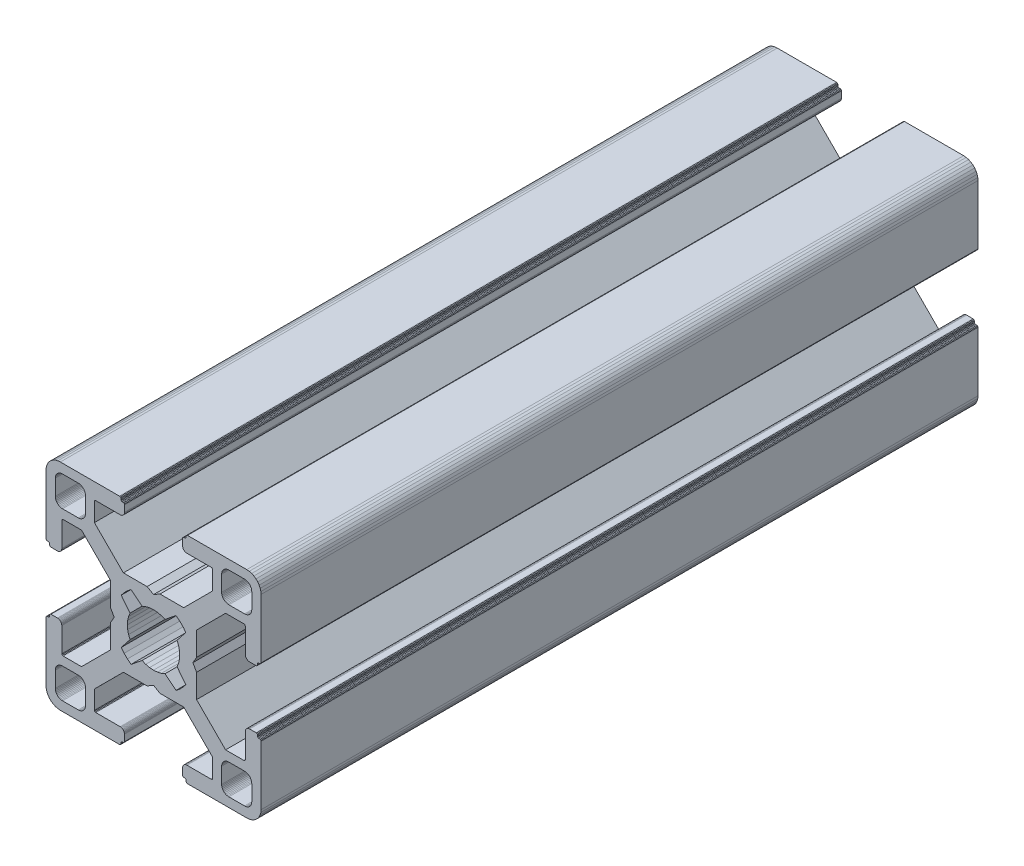
SolidWorks part; units mm, degrees
ref_plane "Front Plane" through (0, 0, 0) normal (0, 0, 1) x (1, 0, 0)
ref_plane "Top Plane" through (0, 0, 0) normal (0, 1, 0) x (1, 0, 0)
ref_plane "Right Plane" through (0, 0, 0) normal (1, 0, 0) x (0, 0, -1)
ref_plane "Plane1" through (0, 0, 0) normal (0, 0, 1) x (1, 0, 0)
sketch "Sketch1" plane through (0, 0, 0) normal (0, 0, 1) x (1, 0, 0)
  line L0 (28.3473, 29.9696) -> (28, 30)
  line L1 (28, 30) -> (19.75, 30)
  line L2 (19.75, 30) -> (19.7153, 29.997)
  line L3 (19.7153, 29.997) -> (19.6816, 29.9879)
  line L4 (19.6816, 29.9879) -> (19.65, 29.9732)
  line L5 (19.65, 29.9732) -> (19.6214, 29.9532)
  line L6 (19.6214, 29.9532) -> (19.5968, 29.9286)
  line L7 (19.5968, 29.9286) -> (19.5768, 29.9)
  line L8 (19.5768, 29.9) -> (19.5621, 29.8684)
  line L9 (19.5621, 29.8684) -> (19.553, 29.8347)
  line L10 (19.553, 29.8347) -> (19.55, 29.8)
  line L11 (19.55, 29.8) -> (19.55, 29.7)
  line L12 (19.55, 29.7) -> (19.547, 29.6653)
  line L13 (19.547, 29.6653) -> (19.5379, 29.6316)
  line L14 (19.5379, 29.6316) -> (19.5232, 29.6)
  line L15 (19.5232, 29.6) -> (19.5032, 29.5714)
  line L16 (19.5032, 29.5714) -> (19.4786, 29.5468)
  line L17 (19.4786, 29.5468) -> (19.45, 29.5268)
  line L18 (19.45, 29.5268) -> (19.4184, 29.5121)
  line L19 (19.4184, 29.5121) -> (19.3847, 29.503)
  line L20 (19.3847, 29.503) -> (19.35, 29.5)
  line L21 (19.35, 29.5) -> (19.25, 29.5)
  line L22 (19.25, 29.5) -> (19.2153, 29.497)
  line L23 (19.2153, 29.497) -> (19.1816, 29.4879)
  line L24 (19.1816, 29.4879) -> (19.15, 29.4732)
  line L25 (19.15, 29.4732) -> (19.1214, 29.4532)
  line L26 (19.1214, 29.4532) -> (19.0968, 29.4286)
  line L27 (19.0968, 29.4286) -> (19.0768, 29.4)
  line L28 (19.0768, 29.4) -> (19.0621, 29.3684)
  line L29 (19.0621, 29.3684) -> (19.053, 29.3347)
  line L30 (19.053, 29.3347) -> (19.05, 29.3)
  line L31 (19.05, 29.3) -> (19.05, 28.4)
  line L32 (19.05, 28.4) -> (19.0591, 28.2958)
  line L33 (19.0591, 28.2958) -> (19.0862, 28.1948)
  line L34 (19.0862, 28.1948) -> (19.1304, 28.1)
  line L35 (19.1304, 28.1) -> (19.1904, 28.0143)
  line L36 (19.1904, 28.0143) -> (19.2643, 27.9404)
  line L37 (19.2643, 27.9404) -> (19.35, 27.8804)
  line L38 (19.35, 27.8804) -> (19.4448, 27.8362)
  line L39 (19.4448, 27.8362) -> (19.5458, 27.8091)
  line L40 (19.5458, 27.8091) -> (19.65, 27.8)
  line L41 (19.65, 27.8) -> (23.05, 27.8)
  line L42 (23.05, 27.8) -> (23.0847, 27.7969)
  line L43 (23.0847, 27.7969) -> (23.1184, 27.7879)
  line L44 (23.1184, 27.7879) -> (23.15, 27.7732)
  line L45 (23.15, 27.7732) -> (23.1786, 27.7532)
  line L46 (23.1786, 27.7532) -> (23.2032, 27.7285)
  line L47 (23.2032, 27.7285) -> (23.2232, 27.7)
  line L48 (23.2232, 27.7) -> (23.2379, 27.6684)
  line L49 (23.2379, 27.6684) -> (23.247, 27.6347)
  line L50 (23.247, 27.6347) -> (23.25, 27.6)
  line L51 (23.25, 27.6) -> (23.25, 25.05)
  line L52 (23.25, 25.05) -> (19.2045, 21)
  line L53 (19.2045, 21) -> (15.9, 21)
  line L54 (15.9, 21) -> (15, 20.4848)
  line L55 (15, 20.4848) -> (14.1, 21)
  line L56 (14.1, 21) -> (10.7955, 21)
  line L57 (10.7955, 21) -> (7.9973, 23.8013)
  line L58 (7.9973, 23.8013) -> (6.75, 25.05)
  line L59 (6.75, 25.05) -> (6.75, 27.6)
  line L60 (6.75, 27.6) -> (6.753, 27.6347)
  line L61 (6.753, 27.6347) -> (6.7621, 27.6684)
  line L62 (6.7621, 27.6684) -> (6.7768, 27.7)
  line L63 (6.7768, 27.7) -> (6.7968, 27.7285)
  line L64 (6.7968, 27.7285) -> (6.8215, 27.7532)
  line L65 (6.8215, 27.7532) -> (6.85, 27.7732)
  line L66 (6.85, 27.7732) -> (6.8816, 27.7879)
  line L67 (6.8816, 27.7879) -> (6.9153, 27.7969)
  line L68 (6.9153, 27.7969) -> (6.95, 27.8)
  line L69 (6.95, 27.8) -> (10.35, 27.8)
  line L70 (10.35, 27.8) -> (10.4542, 27.8091)
  line L71 (10.4542, 27.8091) -> (10.5552, 27.8362)
  line L72 (10.5552, 27.8362) -> (10.65, 27.8804)
  line L73 (10.65, 27.8804) -> (10.7357, 27.9404)
  line L74 (10.7357, 27.9404) -> (10.8096, 28.0143)
  line L75 (10.8096, 28.0143) -> (10.8696, 28.1)
  line L76 (10.8696, 28.1) -> (10.9138, 28.1948)
  line L77 (10.9138, 28.1948) -> (10.9409, 28.2958)
  line L78 (10.9409, 28.2958) -> (10.95, 28.4)
  line L79 (10.95, 28.4) -> (10.95, 29.3)
  line L80 (10.95, 29.3) -> (10.947, 29.3347)
  line L81 (10.947, 29.3347) -> (10.938, 29.3684)
  line L82 (10.938, 29.3684) -> (10.9232, 29.4)
  line L83 (10.9232, 29.4) -> (10.9032, 29.4286)
  line L84 (10.9032, 29.4286) -> (10.8786, 29.4532)
  line L85 (10.8786, 29.4532) -> (10.85, 29.4732)
  line L86 (10.85, 29.4732) -> (10.8184, 29.4879)
  line L87 (10.8184, 29.4879) -> (10.7847, 29.497)
  line L88 (10.7847, 29.497) -> (10.75, 29.5)
  line L89 (10.75, 29.5) -> (10.65, 29.5)
  line L90 (10.65, 29.5) -> (10.6153, 29.503)
  line L91 (10.6153, 29.503) -> (10.5816, 29.5121)
  line L92 (10.5816, 29.5121) -> (10.55, 29.5268)
  line L93 (10.55, 29.5268) -> (10.5214, 29.5468)
  line L94 (10.5214, 29.5468) -> (10.4968, 29.5714)
  line L95 (10.4968, 29.5714) -> (10.4768, 29.6)
  line L96 (10.4768, 29.6) -> (10.4621, 29.6316)
  line L97 (10.4621, 29.6316) -> (10.453, 29.6653)
  line L98 (10.453, 29.6653) -> (10.45, 29.7)
  line L99 (10.45, 29.7) -> (10.45, 29.8)
  line L100 (10.45, 29.8) -> (10.447, 29.8347)
  line L101 (10.447, 29.8347) -> (10.4379, 29.8684)
  line L102 (10.4379, 29.8684) -> (10.4232, 29.9)
  line L103 (10.4232, 29.9) -> (10.4032, 29.9286)
  line L104 (10.4032, 29.9286) -> (10.3786, 29.9532)
  line L105 (10.3786, 29.9532) -> (10.35, 29.9732)
  line L106 (10.35, 29.9732) -> (10.3184, 29.9879)
  line L107 (10.3184, 29.9879) -> (10.2847, 29.997)
  line L108 (10.2847, 29.997) -> (10.25, 30)
  line L109 (10.25, 30) -> (2, 30)
  line L110 (2, 30) -> (1.6527, 29.9696)
  line L111 (1.6527, 29.9696) -> (1.316, 29.8794)
  line L112 (1.316, 29.8794) -> (1, 29.7321)
  line L113 (1, 29.7321) -> (0.7144, 29.5321)
  line L114 (0.7144, 29.5321) -> (0.4679, 29.2856)
  line L115 (0.4679, 29.2856) -> (0.2679, 29)
  line L116 (0.2679, 29) -> (0.1206, 28.684)
  line L117 (0.1206, 28.684) -> (0.0304, 28.3473)
  line L118 (0.0304, 28.3473) -> (0, 28)
  line L119 (0, 28) -> (0, 19.75)
  line L120 (0, 19.75) -> (0.003, 19.7153)
  line L121 (0.003, 19.7153) -> (0.0121, 19.6816)
  line L122 (0.0121, 19.6816) -> (0.0268, 19.65)
  line L123 (0.0268, 19.65) -> (0.0468, 19.6214)
  line L124 (0.0468, 19.6214) -> (0.0714, 19.5968)
  line L125 (0.0714, 19.5968) -> (0.1, 19.5768)
  line L126 (0.1, 19.5768) -> (0.1316, 19.5621)
  line L127 (0.1316, 19.5621) -> (0.1653, 19.553)
  line L128 (0.1653, 19.553) -> (0.2, 19.55)
  line L129 (0.2, 19.55) -> (0.3, 19.55)
  line L130 (0.3, 19.55) -> (0.3347, 19.547)
  line L131 (0.3347, 19.547) -> (0.3684, 19.5379)
  line L132 (0.3684, 19.5379) -> (0.4, 19.5232)
  line L133 (0.4, 19.5232) -> (0.4286, 19.5032)
  line L134 (0.4286, 19.5032) -> (0.4532, 19.4786)
  line L135 (0.4532, 19.4786) -> (0.4732, 19.45)
  line L136 (0.4732, 19.45) -> (0.4879, 19.4184)
  line L137 (0.4879, 19.4184) -> (0.497, 19.3847)
  line L138 (0.497, 19.3847) -> (0.5, 19.35)
  line L139 (0.5, 19.35) -> (0.5, 19.25)
  line L140 (0.5, 19.25) -> (0.503, 19.2153)
  line L141 (0.503, 19.2153) -> (0.5121, 19.1816)
  line L142 (0.5121, 19.1816) -> (0.5268, 19.15)
  line L143 (0.5268, 19.15) -> (0.5468, 19.1214)
  line L144 (0.5468, 19.1214) -> (0.5714, 19.0968)
  line L145 (0.5714, 19.0968) -> (0.6, 19.0768)
  line L146 (0.6, 19.0768) -> (0.6316, 19.0621)
  line L147 (0.6316, 19.0621) -> (0.6653, 19.053)
  line L148 (0.6653, 19.053) -> (0.7, 19.05)
  line L149 (0.7, 19.05) -> (1.6, 19.05)
  line L150 (1.6, 19.05) -> (1.7042, 19.0591)
  line L151 (1.7042, 19.0591) -> (1.8052, 19.0862)
  line L152 (1.8052, 19.0862) -> (1.9, 19.1304)
  line L153 (1.9, 19.1304) -> (1.9857, 19.1904)
  line L154 (1.9857, 19.1904) -> (2.0596, 19.2643)
  line L155 (2.0596, 19.2643) -> (2.1196, 19.35)
  line L156 (2.1196, 19.35) -> (2.1638, 19.4448)
  line L157 (2.1638, 19.4448) -> (2.1909, 19.5458)
  line L158 (2.1909, 19.5458) -> (2.2, 19.65)
  line L159 (2.2, 19.65) -> (2.2, 23.05)
  line L160 (2.2, 23.05) -> (2.203, 23.0847)
  line L161 (2.203, 23.0847) -> (2.2121, 23.1184)
  line L162 (2.2121, 23.1184) -> (2.2268, 23.15)
  line L163 (2.2268, 23.15) -> (2.2468, 23.1786)
  line L164 (2.2468, 23.1786) -> (2.2714, 23.2032)
  line L165 (2.2714, 23.2032) -> (2.3, 23.2232)
  line L166 (2.3, 23.2232) -> (2.3316, 23.2379)
  line L167 (2.3316, 23.2379) -> (2.3653, 23.247)
  line L168 (2.3653, 23.247) -> (2.4, 23.25)
  line L169 (2.4, 23.25) -> (4.95, 23.25)
  line L170 (4.95, 23.25) -> (7.9973, 20.2027)
  line L171 (7.9973, 20.2027) -> (8.9955, 19.2045)
  line L172 (8.9955, 19.2045) -> (8.9955, 15.9)
  line L173 (8.9955, 15.9) -> (9.5151, 15)
  line L174 (9.5151, 15) -> (8.9955, 14.1)
  line L175 (8.9955, 14.1) -> (8.9955, 10.7955)
  line L176 (8.9955, 10.7955) -> (4.95, 6.75)
  line L177 (4.95, 6.75) -> (2.4, 6.75)
  line L178 (2.4, 6.75) -> (2.3653, 6.753)
  line L179 (2.3653, 6.753) -> (2.3316, 6.7621)
  line L180 (2.3316, 6.7621) -> (2.3, 6.7768)
  line L181 (2.3, 6.7768) -> (2.2714, 6.7968)
  line L182 (2.2714, 6.7968) -> (2.2468, 6.8214)
  line L183 (2.2468, 6.8214) -> (2.2268, 6.85)
  line L184 (2.2268, 6.85) -> (2.2121, 6.8816)
  line L185 (2.2121, 6.8816) -> (2.203, 6.9153)
  line L186 (2.203, 6.9153) -> (2.2, 6.95)
  line L187 (2.2, 6.95) -> (2.2, 10.35)
  line L188 (2.2, 10.35) -> (2.1909, 10.4542)
  line L189 (2.1909, 10.4542) -> (2.1638, 10.5552)
  line L190 (2.1638, 10.5552) -> (2.1196, 10.65)
  line L191 (2.1196, 10.65) -> (2.0596, 10.7357)
  line L192 (2.0596, 10.7357) -> (1.9857, 10.8096)
  line L193 (1.9857, 10.8096) -> (1.9, 10.8696)
  line L194 (1.9, 10.8696) -> (1.8052, 10.9138)
  line L195 (1.8052, 10.9138) -> (1.7042, 10.9409)
  line L196 (1.7042, 10.9409) -> (1.6, 10.95)
  line L197 (1.6, 10.95) -> (0.7, 10.95)
  line L198 (0.7, 10.95) -> (0.6653, 10.9469)
  line L199 (0.6653, 10.9469) -> (0.6316, 10.9379)
  line L200 (0.6316, 10.9379) -> (0.6, 10.9232)
  line L201 (0.6, 10.9232) -> (0.5715, 10.9032)
  line L202 (0.5715, 10.9032) -> (0.5468, 10.8785)
  line L203 (0.5468, 10.8785) -> (0.5268, 10.85)
  line L204 (0.5268, 10.85) -> (0.5121, 10.8184)
  line L205 (0.5121, 10.8184) -> (0.503, 10.7847)
  line L206 (0.503, 10.7847) -> (0.5, 10.75)
  line L207 (0.5, 10.75) -> (0.5, 10.65)
  line L208 (0.5, 10.65) -> (0.497, 10.6153)
  line L209 (0.497, 10.6153) -> (0.4879, 10.5816)
  line L210 (0.4879, 10.5816) -> (0.4732, 10.55)
  line L211 (0.4732, 10.55) -> (0.4532, 10.5214)
  line L212 (0.4532, 10.5214) -> (0.4286, 10.4968)
  line L213 (0.4286, 10.4968) -> (0.4, 10.4768)
  line L214 (0.4, 10.4768) -> (0.3684, 10.4621)
  line L215 (0.3684, 10.4621) -> (0.3347, 10.453)
  line L216 (0.3347, 10.453) -> (0.3, 10.45)
  line L217 (0.3, 10.45) -> (0.2, 10.45)
  line L218 (0.2, 10.45) -> (0.1653, 10.447)
  line L219 (0.1653, 10.447) -> (0.1316, 10.4379)
  line L220 (0.1316, 10.4379) -> (0.1, 10.4232)
  line L221 (0.1, 10.4232) -> (0.0714, 10.4032)
  line L222 (0.0714, 10.4032) -> (0.0468, 10.3786)
  line L223 (0.0468, 10.3786) -> (0.0268, 10.35)
  line L224 (0.0268, 10.35) -> (0.0121, 10.3184)
  line L225 (0.0121, 10.3184) -> (0.003, 10.2847)
  line L226 (0.003, 10.2847) -> (0, 10.25)
  line L227 (0, 10.25) -> (0, 2)
  line L228 (0, 2) -> (0.0304, 1.6527)
  line L229 (0.0304, 1.6527) -> (0.1206, 1.316)
  line L230 (0.1206, 1.316) -> (0.2679, 1)
  line L231 (0.2679, 1) -> (0.4679, 0.7144)
  line L232 (0.4679, 0.7144) -> (0.7144, 0.4679)
  line L233 (0.7144, 0.4679) -> (1, 0.2679)
  line L234 (1, 0.2679) -> (1.316, 0.1206)
  line L235 (1.316, 0.1206) -> (1.6527, 0.0304)
  line L236 (1.6527, 0.0304) -> (2, 0)
  line L237 (2, 0) -> (10.25, 0)
  line L238 (10.25, 0) -> (10.2847, 0.003)
  line L239 (10.2847, 0.003) -> (10.3184, 0.0121)
  line L240 (10.3184, 0.0121) -> (10.35, 0.0268)
  line L241 (10.35, 0.0268) -> (10.3786, 0.0468)
  line L242 (10.3786, 0.0468) -> (10.4032, 0.0714)
  line L243 (10.4032, 0.0714) -> (10.4232, 0.1)
  line L244 (10.4232, 0.1) -> (10.4379, 0.1316)
  line L245 (10.4379, 0.1316) -> (10.447, 0.1653)
  line L246 (10.447, 0.1653) -> (10.45, 0.2)
  line L247 (10.45, 0.2) -> (10.45, 0.3)
  line L248 (10.45, 0.3) -> (10.453, 0.3347)
  line L249 (10.453, 0.3347) -> (10.4621, 0.3684)
  line L250 (10.4621, 0.3684) -> (10.4768, 0.4)
  line L251 (10.4768, 0.4) -> (10.4968, 0.4286)
  line L252 (10.4968, 0.4286) -> (10.5214, 0.4532)
  line L253 (10.5214, 0.4532) -> (10.55, 0.4732)
  line L254 (10.55, 0.4732) -> (10.5816, 0.4879)
  line L255 (10.5816, 0.4879) -> (10.6153, 0.497)
  line L256 (10.6153, 0.497) -> (10.65, 0.5)
  line L257 (10.65, 0.5) -> (10.75, 0.5)
  line L258 (10.75, 0.5) -> (10.7847, 0.503)
  line L259 (10.7847, 0.503) -> (10.8184, 0.5121)
  line L260 (10.8184, 0.5121) -> (10.85, 0.5268)
  line L261 (10.85, 0.5268) -> (10.8785, 0.5468)
  line L262 (10.8785, 0.5468) -> (10.9032, 0.5715)
  line L263 (10.9032, 0.5715) -> (10.9232, 0.6)
  line L264 (10.9232, 0.6) -> (10.9379, 0.6316)
  line L265 (10.9379, 0.6316) -> (10.9469, 0.6653)
  line L266 (10.9469, 0.6653) -> (10.95, 0.7)
  line L267 (10.95, 0.7) -> (10.95, 1.6)
  line L268 (10.95, 1.6) -> (10.9409, 1.7042)
  line L269 (10.9409, 1.7042) -> (10.9138, 1.8052)
  line L270 (10.9138, 1.8052) -> (10.8696, 1.9)
  line L271 (10.8696, 1.9) -> (10.8096, 1.9857)
  line L272 (10.8096, 1.9857) -> (10.7357, 2.0596)
  line L273 (10.7357, 2.0596) -> (10.65, 2.1196)
  line L274 (10.65, 2.1196) -> (10.5552, 2.1638)
  line L275 (10.5552, 2.1638) -> (10.4542, 2.1909)
  line L276 (10.4542, 2.1909) -> (10.35, 2.2)
  line L277 (10.35, 2.2) -> (6.95, 2.2)
  line L278 (6.95, 2.2) -> (6.9153, 2.203)
  line L279 (6.9153, 2.203) -> (6.8816, 2.212)
  line L280 (6.8816, 2.212) -> (6.85, 2.2268)
  line L281 (6.85, 2.2268) -> (6.8215, 2.2468)
  line L282 (6.8215, 2.2468) -> (6.7968, 2.2714)
  line L283 (6.7968, 2.2714) -> (6.7768, 2.3)
  line L284 (6.7768, 2.3) -> (6.7621, 2.3316)
  line L285 (6.7621, 2.3316) -> (6.753, 2.3653)
  line L286 (6.753, 2.3653) -> (6.75, 2.4)
  line L287 (6.75, 2.4) -> (6.75, 4.95)
  line L288 (6.75, 4.95) -> (9.7875, 7.9908)
  line L289 (9.7875, 7.9908) -> (10.7955, 9)
  line L290 (10.7955, 9) -> (14.1, 9)
  line L291 (14.1, 9) -> (15, 9.5151)
  line L292 (15, 9.5151) -> (15.9, 9)
  line L293 (15.9, 9) -> (19.2045, 9)
  line L294 (19.2045, 9) -> (20.2126, 7.9908)
  line L295 (20.2126, 7.9908) -> (23.25, 4.95)
  line L296 (23.25, 4.95) -> (23.25, 2.4)
  line L297 (23.25, 2.4) -> (23.247, 2.3653)
  line L298 (23.247, 2.3653) -> (23.2379, 2.3316)
  line L299 (23.2379, 2.3316) -> (23.2232, 2.3)
  line L300 (23.2232, 2.3) -> (23.2032, 2.2714)
  line L301 (23.2032, 2.2714) -> (23.1786, 2.2468)
  line L302 (23.1786, 2.2468) -> (23.15, 2.2268)
  line L303 (23.15, 2.2268) -> (23.1184, 2.212)
  line L304 (23.1184, 2.212) -> (23.0847, 2.203)
  line L305 (23.0847, 2.203) -> (23.05, 2.2)
  line L306 (23.05, 2.2) -> (19.65, 2.2)
  line L307 (19.65, 2.2) -> (19.5458, 2.1909)
  line L308 (19.5458, 2.1909) -> (19.4448, 2.1638)
  line L309 (19.4448, 2.1638) -> (19.35, 2.1196)
  line L310 (19.35, 2.1196) -> (19.2643, 2.0596)
  line L311 (19.2643, 2.0596) -> (19.1904, 1.9857)
  line L312 (19.1904, 1.9857) -> (19.1304, 1.9)
  line L313 (19.1304, 1.9) -> (19.0862, 1.8052)
  line L314 (19.0862, 1.8052) -> (19.0591, 1.7042)
  line L315 (19.0591, 1.7042) -> (19.05, 1.6)
  line L316 (19.05, 1.6) -> (19.05, 0.7)
  line L317 (19.05, 0.7) -> (19.053, 0.6653)
  line L318 (19.053, 0.6653) -> (19.0621, 0.6316)
  line L319 (19.0621, 0.6316) -> (19.0768, 0.6)
  line L320 (19.0768, 0.6) -> (19.0968, 0.5714)
  line L321 (19.0968, 0.5714) -> (19.1214, 0.5468)
  line L322 (19.1214, 0.5468) -> (19.15, 0.5268)
  line L323 (19.15, 0.5268) -> (19.1816, 0.5121)
  line L324 (19.1816, 0.5121) -> (19.2153, 0.503)
  line L325 (19.2153, 0.503) -> (19.25, 0.5)
  line L326 (19.25, 0.5) -> (19.35, 0.5)
  line L327 (19.35, 0.5) -> (19.3847, 0.497)
  line L328 (19.3847, 0.497) -> (19.4184, 0.4879)
  line L329 (19.4184, 0.4879) -> (19.45, 0.4732)
  line L330 (19.45, 0.4732) -> (19.4786, 0.4532)
  line L331 (19.4786, 0.4532) -> (19.5032, 0.4286)
  line L332 (19.5032, 0.4286) -> (19.5232, 0.4)
  line L333 (19.5232, 0.4) -> (19.5379, 0.3684)
  line L334 (19.5379, 0.3684) -> (19.547, 0.3347)
  line L335 (19.547, 0.3347) -> (19.55, 0.3)
  line L336 (19.55, 0.3) -> (19.55, 0.2)
  line L337 (19.55, 0.2) -> (19.553, 0.1653)
  line L338 (19.553, 0.1653) -> (19.5621, 0.1316)
  line L339 (19.5621, 0.1316) -> (19.5768, 0.1)
  line L340 (19.5768, 0.1) -> (19.5968, 0.0714)
  line L341 (19.5968, 0.0714) -> (19.6214, 0.0468)
  line L342 (19.6214, 0.0468) -> (19.65, 0.0268)
  line L343 (19.65, 0.0268) -> (19.6816, 0.0121)
  line L344 (19.6816, 0.0121) -> (19.7153, 0.003)
  line L345 (19.7153, 0.003) -> (19.75, 0)
  line L346 (19.75, 0) -> (28, 0)
  line L347 (28, 0) -> (28.3473, 0.0304)
  line L348 (28.3473, 0.0304) -> (28.684, 0.1206)
  line L349 (28.684, 0.1206) -> (29, 0.2679)
  line L350 (29, 0.2679) -> (29.2856, 0.4679)
  line L351 (29.2856, 0.4679) -> (29.5321, 0.7144)
  line L352 (29.5321, 0.7144) -> (29.7321, 1)
  line L353 (29.7321, 1) -> (29.8794, 1.316)
  line L354 (29.8794, 1.316) -> (29.9696, 1.6527)
  line L355 (29.9696, 1.6527) -> (30, 2)
  line L356 (30, 2) -> (30, 10.25)
  line L357 (30, 10.25) -> (29.997, 10.2847)
  line L358 (29.997, 10.2847) -> (29.988, 10.3184)
  line L359 (29.988, 10.3184) -> (29.9732, 10.35)
  line L360 (29.9732, 10.35) -> (29.9532, 10.3785)
  line L361 (29.9532, 10.3785) -> (29.9286, 10.4032)
  line L362 (29.9286, 10.4032) -> (29.9, 10.4232)
  line L363 (29.9, 10.4232) -> (29.8684, 10.4379)
  line L364 (29.8684, 10.4379) -> (29.8347, 10.447)
  line L365 (29.8347, 10.447) -> (29.8, 10.45)
  line L366 (29.8, 10.45) -> (29.7, 10.45)
  line L367 (29.7, 10.45) -> (29.6649, 10.4534)
  line L368 (29.6649, 10.4534) -> (29.6312, 10.4624)
  line L369 (29.6312, 10.4624) -> (29.5996, 10.4772)
  line L370 (29.5996, 10.4772) -> (29.5711, 10.4972)
  line L371 (29.5711, 10.4972) -> (29.5464, 10.5218)
  line L372 (29.5464, 10.5218) -> (29.5264, 10.5504)
  line L373 (29.5264, 10.5504) -> (29.5117, 10.582)
  line L374 (29.5117, 10.582) -> (29.5027, 10.6156)
  line L375 (29.5027, 10.6156) -> (29.4996, 10.6504)
  line L376 (29.4996, 10.6504) -> (29.4996, 10.7504)
  line L377 (29.4996, 10.7504) -> (29.497, 10.7847)
  line L378 (29.497, 10.7847) -> (29.4879, 10.8184)
  line L379 (29.4879, 10.8184) -> (29.4732, 10.85)
  line L380 (29.4732, 10.85) -> (29.4532, 10.8785)
  line L381 (29.4532, 10.8785) -> (29.4286, 10.9032)
  line L382 (29.4286, 10.9032) -> (29.4, 10.9232)
  line L383 (29.4, 10.9232) -> (29.3684, 10.9379)
  line L384 (29.3684, 10.9379) -> (29.3347, 10.9469)
  line L385 (29.3347, 10.9469) -> (29.3, 10.95)
  line L386 (29.3, 10.95) -> (28.4, 10.95)
  line L387 (28.4, 10.95) -> (28.2958, 10.9409)
  line L388 (28.2958, 10.9409) -> (28.1948, 10.9138)
  line L389 (28.1948, 10.9138) -> (28.1, 10.8696)
  line L390 (28.1, 10.8696) -> (28.0143, 10.8096)
  line L391 (28.0143, 10.8096) -> (27.9404, 10.7357)
  line L392 (27.9404, 10.7357) -> (27.8804, 10.65)
  line L393 (27.8804, 10.65) -> (27.8362, 10.5552)
  line L394 (27.8362, 10.5552) -> (27.8091, 10.4542)
  line L395 (27.8091, 10.4542) -> (27.8, 10.35)
  line L396 (27.8, 10.35) -> (27.8, 6.95)
  line L397 (27.8, 6.95) -> (27.797, 6.9153)
  line L398 (27.797, 6.9153) -> (27.7879, 6.8816)
  line L399 (27.7879, 6.8816) -> (27.7732, 6.85)
  line L400 (27.7732, 6.85) -> (27.7532, 6.8214)
  line L401 (27.7532, 6.8214) -> (27.7286, 6.7968)
  line L402 (27.7286, 6.7968) -> (27.7, 6.7768)
  line L403 (27.7, 6.7768) -> (27.6684, 6.7621)
  line L404 (27.6684, 6.7621) -> (27.6347, 6.753)
  line L405 (27.6347, 6.753) -> (27.6, 6.75)
  line L406 (27.6, 6.75) -> (25.05, 6.75)
  line L407 (25.05, 6.75) -> (23.8092, 7.9908)
  line L408 (23.8092, 7.9908) -> (21.0045, 10.7955)
  line L409 (21.0045, 10.7955) -> (21.0045, 14.1)
  line L410 (21.0045, 14.1) -> (20.4849, 15)
  line L411 (20.4849, 15) -> (21.0045, 15.9)
  line L412 (21.0045, 15.9) -> (21.0045, 19.2045)
  line L413 (21.0045, 19.2045) -> (25.05, 23.25)
  line L414 (25.05, 23.25) -> (27.6, 23.25)
  line L415 (27.6, 23.25) -> (27.6347, 23.247)
  line L416 (27.6347, 23.247) -> (27.6684, 23.2379)
  line L417 (27.6684, 23.2379) -> (27.7, 23.2232)
  line L418 (27.7, 23.2232) -> (27.7286, 23.2032)
  line L419 (27.7286, 23.2032) -> (27.7532, 23.1786)
  line L420 (27.7532, 23.1786) -> (27.7732, 23.15)
  line L421 (27.7732, 23.15) -> (27.7879, 23.1184)
  line L422 (27.7879, 23.1184) -> (27.797, 23.0847)
  line L423 (27.797, 23.0847) -> (27.8, 23.05)
  line L424 (27.8, 23.05) -> (27.8, 19.65)
  line L425 (27.8, 19.65) -> (27.8091, 19.5458)
  line L426 (27.8091, 19.5458) -> (27.8362, 19.4448)
  line L427 (27.8362, 19.4448) -> (27.8804, 19.35)
  line L428 (27.8804, 19.35) -> (27.9404, 19.2643)
  line L429 (27.9404, 19.2643) -> (28.0143, 19.1904)
  line L430 (28.0143, 19.1904) -> (28.1, 19.1304)
  line L431 (28.1, 19.1304) -> (28.1948, 19.0862)
  line L432 (28.1948, 19.0862) -> (28.2958, 19.0591)
  line L433 (28.2958, 19.0591) -> (28.4, 19.05)
  line L434 (28.4, 19.05) -> (29.3, 19.05)
  line L435 (29.3, 19.05) -> (29.3347, 19.053)
  line L436 (29.3347, 19.053) -> (29.3684, 19.0621)
  line L437 (29.3684, 19.0621) -> (29.4, 19.0768)
  line L438 (29.4, 19.0768) -> (29.4282, 19.0971)
  line L439 (29.4282, 19.0971) -> (29.4528, 19.1218)
  line L440 (29.4528, 19.1218) -> (29.4728, 19.1504)
  line L441 (29.4728, 19.1504) -> (29.4876, 19.182)
  line L442 (29.4876, 19.182) -> (29.4966, 19.2156)
  line L443 (29.4966, 19.2156) -> (29.4996, 19.2504)
  line L444 (29.4996, 19.2504) -> (29.4996, 19.3504)
  line L445 (29.4996, 19.3504) -> (29.5027, 19.3851)
  line L446 (29.5027, 19.3851) -> (29.5117, 19.4188)
  line L447 (29.5117, 19.4188) -> (29.5264, 19.4504)
  line L448 (29.5264, 19.4504) -> (29.5464, 19.4789)
  line L449 (29.5464, 19.4789) -> (29.5711, 19.5036)
  line L450 (29.5711, 19.5036) -> (29.5996, 19.5236)
  line L451 (29.5996, 19.5236) -> (29.6312, 19.5383)
  line L452 (29.6312, 19.5383) -> (29.6649, 19.5473)
  line L453 (29.6649, 19.5473) -> (29.7, 19.55)
  line L454 (29.7, 19.55) -> (29.8, 19.55)
  line L455 (29.8, 19.55) -> (29.8347, 19.553)
  line L456 (29.8347, 19.553) -> (29.8684, 19.5621)
  line L457 (29.8684, 19.5621) -> (29.9, 19.5768)
  line L458 (29.9, 19.5768) -> (29.9286, 19.5968)
  line L459 (29.9286, 19.5968) -> (29.9532, 19.6214)
  line L460 (29.9532, 19.6214) -> (29.9732, 19.65)
  line L461 (29.9732, 19.65) -> (29.9879, 19.6816)
  line L462 (29.9879, 19.6816) -> (29.997, 19.7153)
  line L463 (29.997, 19.7153) -> (30, 19.75)
  line L464 (30, 19.75) -> (30, 28)
  line L465 (30, 28) -> (29.9696, 28.3473)
  line L466 (29.9696, 28.3473) -> (29.8794, 28.684)
  line L467 (29.8794, 28.684) -> (29.7321, 29)
  line L468 (29.7321, 29) -> (29.5321, 29.2856)
  line L469 (29.5321, 29.2856) -> (29.2856, 29.5321)
  line L470 (29.2856, 29.5321) -> (29, 29.7321)
  line L471 (29, 29.7321) -> (28.684, 29.8794)
  line L472 (28.684, 29.8794) -> (28.3473, 29.9696)
  line L473 (1.3, 25.5) -> (1.3, 27.7)
  line L474 (1.3, 27.7) -> (1.3123, 27.8564)
  line L475 (1.3123, 27.8564) -> (1.3489, 28.009)
  line L476 (1.3489, 28.009) -> (1.409, 28.154)
  line L477 (1.409, 28.154) -> (1.491, 28.2878)
  line L478 (1.491, 28.2878) -> (1.5929, 28.4071)
  line L479 (1.5929, 28.4071) -> (1.7122, 28.509)
  line L480 (1.7122, 28.509) -> (1.846, 28.591)
  line L481 (1.846, 28.591) -> (1.991, 28.6511)
  line L482 (1.991, 28.6511) -> (2.1436, 28.6877)
  line L483 (2.1436, 28.6877) -> (2.3, 28.7)
  line L484 (2.3, 28.7) -> (4.5, 28.7)
  line L485 (4.5, 28.7) -> (4.6564, 28.6877)
  line L486 (4.6564, 28.6877) -> (4.809, 28.6511)
  line L487 (4.809, 28.6511) -> (4.954, 28.591)
  line L488 (4.954, 28.591) -> (5.0878, 28.509)
  line L489 (5.0878, 28.509) -> (5.2071, 28.4071)
  line L490 (5.2071, 28.4071) -> (5.309, 28.2878)
  line L491 (5.309, 28.2878) -> (5.391, 28.154)
  line L492 (5.391, 28.154) -> (5.4511, 28.009)
  line L493 (5.4511, 28.009) -> (5.4877, 27.8564)
  line L494 (5.4877, 27.8564) -> (5.5, 27.7)
  line L495 (5.5, 27.7) -> (5.5, 25.5)
  line L496 (5.5, 25.5) -> (5.4877, 25.3436)
  line L497 (5.4877, 25.3436) -> (5.4511, 25.191)
  line L498 (5.4511, 25.191) -> (5.391, 25.046)
  line L499 (5.391, 25.046) -> (5.309, 24.9122)
  line L500 (5.309, 24.9122) -> (5.2071, 24.7929)
  line L501 (5.2071, 24.7929) -> (5.0878, 24.691)
  line L502 (5.0878, 24.691) -> (4.954, 24.609)
  line L503 (4.954, 24.609) -> (4.809, 24.5489)
  line L504 (4.809, 24.5489) -> (4.6564, 24.5123)
  line L505 (4.6564, 24.5123) -> (4.5, 24.5)
  line L506 (4.5, 24.5) -> (2.3, 24.5)
  line L507 (2.3, 24.5) -> (2.1436, 24.5123)
  line L508 (2.1436, 24.5123) -> (1.991, 24.5489)
  line L509 (1.991, 24.5489) -> (1.846, 24.609)
  line L510 (1.846, 24.609) -> (1.7122, 24.691)
  line L511 (1.7122, 24.691) -> (1.5929, 24.7929)
  line L512 (1.5929, 24.7929) -> (1.491, 24.9122)
  line L513 (1.491, 24.9122) -> (1.409, 25.046)
  line L514 (1.409, 25.046) -> (1.3489, 25.191)
  line L515 (1.3489, 25.191) -> (1.3123, 25.3436)
  line L516 (1.3123, 25.3436) -> (1.3, 25.5)
  line L517 (25.3436, 28.6877) -> (25.5, 28.7)
  line L518 (25.5, 28.7) -> (27.7, 28.7)
  line L519 (27.7, 28.7) -> (27.8564, 28.6877)
  line L520 (27.8564, 28.6877) -> (28.009, 28.6511)
  line L521 (28.009, 28.6511) -> (28.154, 28.591)
  line L522 (28.154, 28.591) -> (28.2878, 28.509)
  line L523 (28.2878, 28.509) -> (28.4071, 28.4071)
  line L524 (28.4071, 28.4071) -> (28.509, 28.2878)
  line L525 (28.509, 28.2878) -> (28.591, 28.154)
  line L526 (28.591, 28.154) -> (28.6511, 28.009)
  line L527 (28.6511, 28.009) -> (28.6877, 27.8564)
  line L528 (28.6877, 27.8564) -> (28.7, 27.7)
  line L529 (28.7, 27.7) -> (28.7, 25.5)
  line L530 (28.7, 25.5) -> (28.6877, 25.3436)
  line L531 (28.6877, 25.3436) -> (28.6511, 25.191)
  line L532 (28.6511, 25.191) -> (28.591, 25.046)
  line L533 (28.591, 25.046) -> (28.509, 24.9122)
  line L534 (28.509, 24.9122) -> (28.4071, 24.7929)
  line L535 (28.4071, 24.7929) -> (28.2878, 24.691)
  line L536 (28.2878, 24.691) -> (28.154, 24.609)
  line L537 (28.154, 24.609) -> (28.009, 24.5489)
  line L538 (28.009, 24.5489) -> (27.8564, 24.5123)
  line L539 (27.8564, 24.5123) -> (27.7, 24.5)
  line L540 (27.7, 24.5) -> (25.5, 24.5)
  line L541 (25.5, 24.5) -> (25.3436, 24.5123)
  line L542 (25.3436, 24.5123) -> (25.191, 24.5489)
  line L543 (25.191, 24.5489) -> (25.046, 24.609)
  line L544 (25.046, 24.609) -> (24.9122, 24.691)
  line L545 (24.9122, 24.691) -> (24.7929, 24.7929)
  line L546 (24.7929, 24.7929) -> (24.691, 24.9122)
  line L547 (24.691, 24.9122) -> (24.609, 25.046)
  line L548 (24.609, 25.046) -> (24.5489, 25.191)
  line L549 (24.5489, 25.191) -> (24.5123, 25.3436)
  line L550 (24.5123, 25.3436) -> (24.5, 25.5)
  line L551 (24.5, 25.5) -> (24.5, 27.7)
  line L552 (24.5, 27.7) -> (24.5123, 27.8564)
  line L553 (24.5123, 27.8564) -> (24.5489, 28.009)
  line L554 (24.5489, 28.009) -> (24.609, 28.154)
  line L555 (24.609, 28.154) -> (24.691, 28.2878)
  line L556 (24.691, 28.2878) -> (24.7929, 28.4071)
  line L557 (24.7929, 28.4071) -> (24.9122, 28.509)
  line L558 (24.9122, 28.509) -> (25.046, 28.591)
  line L559 (25.046, 28.591) -> (25.191, 28.6511)
  line L560 (25.191, 28.6511) -> (25.3436, 28.6877)
  line L561 (15, 18.65) -> (15.55, 18.6083)
  line L562 (15.55, 18.6083) -> (16.0875, 18.4842)
  line L563 (16.0875, 18.4842) -> (16.6001, 18.2806)
  line L564 (16.6001, 18.2806) -> (18.1359, 19.5184)
  line L565 (18.1359, 19.5184) -> (18.645, 19.1187)
  line L566 (18.645, 19.1187) -> (19.1036, 18.6621)
  line L567 (19.1036, 18.6621) -> (19.5053, 18.1547)
  line L568 (19.5053, 18.1547) -> (18.2806, 16.6001)
  line L569 (18.2806, 16.6001) -> (18.4842, 16.0875)
  line L570 (18.4842, 16.0875) -> (18.6083, 15.55)
  line L571 (18.6083, 15.55) -> (18.65, 15)
  line L572 (18.65, 15) -> (18.6083, 14.45)
  line L573 (18.6083, 14.45) -> (18.4842, 13.9125)
  line L574 (18.4842, 13.9125) -> (18.2806, 13.3999)
  line L575 (18.2806, 13.3999) -> (19.5053, 11.8453)
  line L576 (19.5053, 11.8453) -> (19.1036, 11.3379)
  line L577 (19.1036, 11.3379) -> (18.645, 10.8813)
  line L578 (18.645, 10.8813) -> (18.1359, 10.4816)
  line L579 (18.1359, 10.4816) -> (16.6001, 11.7194)
  line L580 (16.6001, 11.7194) -> (16.0875, 11.5158)
  line L581 (16.0875, 11.5158) -> (15.55, 11.3917)
  line L582 (15.55, 11.3917) -> (15, 11.35)
  line L583 (15, 11.35) -> (14.45, 11.3917)
  line L584 (14.45, 11.3917) -> (13.9125, 11.5158)
  line L585 (13.9125, 11.5158) -> (13.3999, 11.7194)
  line L586 (13.3999, 11.7194) -> (11.8641, 10.4816)
  line L587 (11.8641, 10.4816) -> (11.355, 10.8813)
  line L588 (11.355, 10.8813) -> (10.8964, 11.3379)
  line L589 (10.8964, 11.3379) -> (10.4947, 11.8453)
  line L590 (10.4947, 11.8453) -> (11.7194, 13.3999)
  line L591 (11.7194, 13.3999) -> (11.5158, 13.9125)
  line L592 (11.5158, 13.9125) -> (11.3917, 14.45)
  line L593 (11.3917, 14.45) -> (11.35, 15)
  line L594 (11.35, 15) -> (11.3917, 15.55)
  line L595 (11.3917, 15.55) -> (11.5158, 16.0875)
  line L596 (11.5158, 16.0875) -> (11.7194, 16.6001)
  line L597 (11.7194, 16.6001) -> (10.4947, 18.1547)
  line L598 (10.4947, 18.1547) -> (10.8964, 18.6621)
  line L599 (10.8964, 18.6621) -> (11.355, 19.1187)
  line L600 (11.355, 19.1187) -> (11.8641, 19.5184)
  line L601 (11.8641, 19.5184) -> (13.3999, 18.2806)
  line L602 (13.3999, 18.2806) -> (13.9125, 18.4842)
  line L603 (13.9125, 18.4842) -> (14.45, 18.6083)
  line L604 (14.45, 18.6083) -> (15, 18.65)
  line L605 (4.5, 1.3) -> (2.3, 1.3)
  line L606 (2.3, 1.3) -> (2.1436, 1.3123)
  line L607 (2.1436, 1.3123) -> (1.991, 1.3489)
  line L608 (1.991, 1.3489) -> (1.846, 1.409)
  line L609 (1.846, 1.409) -> (1.7122, 1.491)
  line L610 (1.7122, 1.491) -> (1.5929, 1.5929)
  line L611 (1.5929, 1.5929) -> (1.491, 1.7122)
  line L612 (1.491, 1.7122) -> (1.409, 1.846)
  line L613 (1.409, 1.846) -> (1.3489, 1.991)
  line L614 (1.3489, 1.991) -> (1.3123, 2.1436)
  line L615 (1.3123, 2.1436) -> (1.3, 2.3)
  line L616 (1.3, 2.3) -> (1.3, 4.5)
  line L617 (1.3, 4.5) -> (1.3123, 4.6564)
  line L618 (1.3123, 4.6564) -> (1.3489, 4.809)
  line L619 (1.3489, 4.809) -> (1.409, 4.954)
  line L620 (1.409, 4.954) -> (1.491, 5.0878)
  line L621 (1.491, 5.0878) -> (1.5929, 5.2071)
  line L622 (1.5929, 5.2071) -> (1.7122, 5.309)
  line L623 (1.7122, 5.309) -> (1.846, 5.391)
  line L624 (1.846, 5.391) -> (1.991, 5.4511)
  line L625 (1.991, 5.4511) -> (2.1436, 5.4877)
  line L626 (2.1436, 5.4877) -> (2.3, 5.5)
  line L627 (2.3, 5.5) -> (4.5, 5.5)
  line L628 (4.5, 5.5) -> (4.6564, 5.4877)
  line L629 (4.6564, 5.4877) -> (4.809, 5.4511)
  line L630 (4.809, 5.4511) -> (4.954, 5.391)
  line L631 (4.954, 5.391) -> (5.0878, 5.309)
  line L632 (5.0878, 5.309) -> (5.2071, 5.2071)
  line L633 (5.2071, 5.2071) -> (5.309, 5.0878)
  line L634 (5.309, 5.0878) -> (5.391, 4.954)
  line L635 (5.391, 4.954) -> (5.4511, 4.809)
  line L636 (5.4511, 4.809) -> (5.4877, 4.6564)
  line L637 (5.4877, 4.6564) -> (5.5, 4.5)
  line L638 (5.5, 4.5) -> (5.5, 2.3)
  line L639 (5.5, 2.3) -> (5.4877, 2.1436)
  line L640 (5.4877, 2.1436) -> (5.4511, 1.991)
  line L641 (5.4511, 1.991) -> (5.391, 1.846)
  line L642 (5.391, 1.846) -> (5.309, 1.7122)
  line L643 (5.309, 1.7122) -> (5.2071, 1.5929)
  line L644 (5.2071, 1.5929) -> (5.0878, 1.491)
  line L645 (5.0878, 1.491) -> (4.954, 1.409)
  line L646 (4.954, 1.409) -> (4.809, 1.3489)
  line L647 (4.809, 1.3489) -> (4.6564, 1.3123)
  line L648 (4.6564, 1.3123) -> (4.5, 1.3)
  line L649 (27.7, 1.3) -> (25.5, 1.3)
  line L650 (25.5, 1.3) -> (25.3436, 1.3123)
  line L651 (25.3436, 1.3123) -> (25.191, 1.3489)
  line L652 (25.191, 1.3489) -> (25.046, 1.409)
  line L653 (25.046, 1.409) -> (24.9122, 1.491)
  line L654 (24.9122, 1.491) -> (24.7929, 1.5929)
  line L655 (24.7929, 1.5929) -> (24.691, 1.7122)
  line L656 (24.691, 1.7122) -> (24.609, 1.846)
  line L657 (24.609, 1.846) -> (24.5489, 1.991)
  line L658 (24.5489, 1.991) -> (24.5123, 2.1436)
  line L659 (24.5123, 2.1436) -> (24.5, 2.3)
  line L660 (24.5, 2.3) -> (24.5, 4.5)
  line L661 (24.5, 4.5) -> (24.5123, 4.6564)
  line L662 (24.5123, 4.6564) -> (24.5489, 4.809)
  line L663 (24.5489, 4.809) -> (24.609, 4.954)
  line L664 (24.609, 4.954) -> (24.691, 5.0878)
  line L665 (24.691, 5.0878) -> (24.7929, 5.2071)
  line L666 (24.7929, 5.2071) -> (24.9122, 5.309)
  line L667 (24.9122, 5.309) -> (25.046, 5.391)
  line L668 (25.046, 5.391) -> (25.191, 5.4511)
  line L669 (25.191, 5.4511) -> (25.3436, 5.4877)
  line L670 (25.3436, 5.4877) -> (25.5, 5.5)
  line L671 (25.5, 5.5) -> (27.7, 5.5)
  line L672 (27.7, 5.5) -> (27.8564, 5.4877)
  line L673 (27.8564, 5.4877) -> (28.009, 5.4511)
  line L674 (28.009, 5.4511) -> (28.154, 5.391)
  line L675 (28.154, 5.391) -> (28.2878, 5.309)
  line L676 (28.2878, 5.309) -> (28.4071, 5.2071)
  line L677 (28.4071, 5.2071) -> (28.509, 5.0878)
  line L678 (28.509, 5.0878) -> (28.591, 4.954)
  line L679 (28.591, 4.954) -> (28.6511, 4.809)
  line L680 (28.6511, 4.809) -> (28.6877, 4.6564)
  line L681 (28.6877, 4.6564) -> (28.7, 4.5)
  line L682 (28.7, 4.5) -> (28.7, 2.3)
  line L683 (28.7, 2.3) -> (28.6877, 2.1436)
  line L684 (28.6877, 2.1436) -> (28.6511, 1.991)
  line L685 (28.6511, 1.991) -> (28.591, 1.846)
  line L686 (28.591, 1.846) -> (28.509, 1.7122)
  line L687 (28.509, 1.7122) -> (28.4071, 1.5929)
  line L688 (28.4071, 1.5929) -> (28.2878, 1.491)
  line L689 (28.2878, 1.491) -> (28.154, 1.409)
  line L690 (28.154, 1.409) -> (28.009, 1.3489)
  line L691 (28.009, 1.3489) -> (27.8564, 1.3123)
  line L692 (27.8564, 1.3123) -> (27.7, 1.3)
extrude "Boss-Extrude1" add sketch "Sketch1" against normal blind 100
